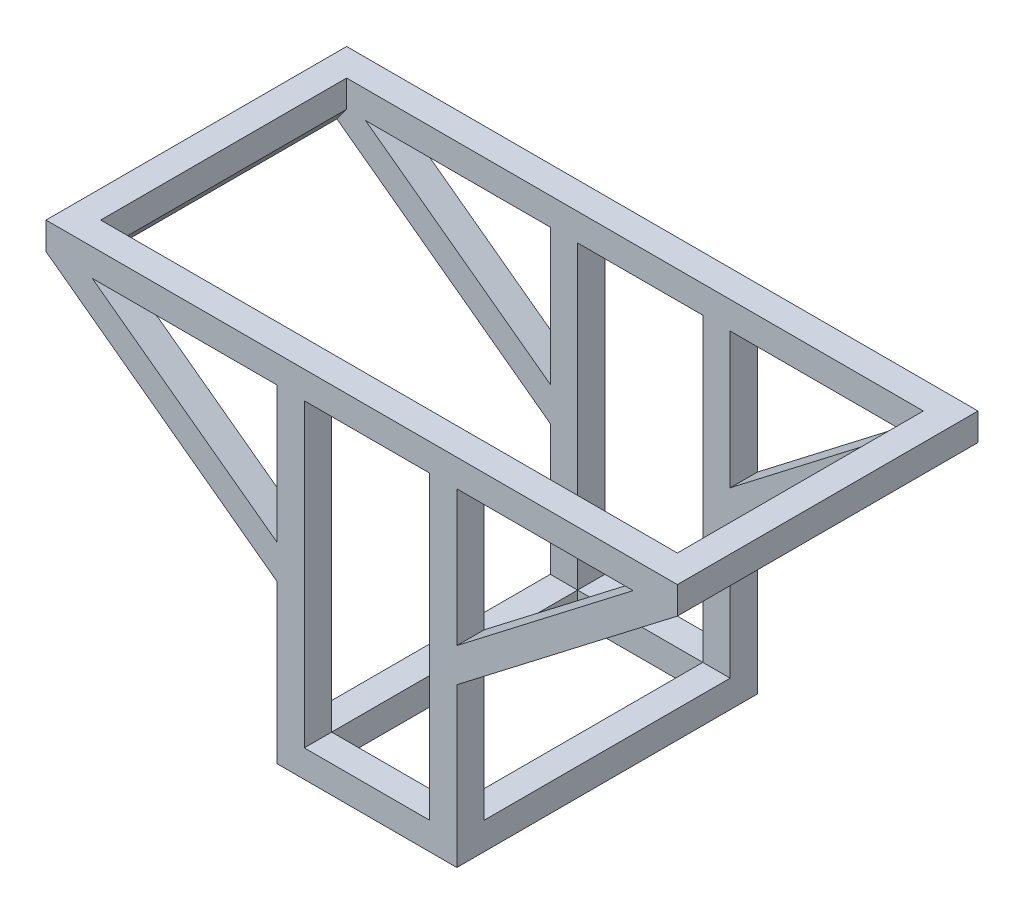
SolidWorks part; units mm, degrees
ref_plane "Front Plane" through (0, 0, 0) normal (0, 0, 1) x (1, 0, 0)
ref_plane "Top Plane" through (0, 0, 0) normal (0, 1, 0) x (1, 0, 0)
ref_plane "Right Plane" through (0, 0, 0) normal (1, 0, 0) x (0, 0, -1)
sketch "Sketch3" plane through (0, 0, 0) normal (0, 0, 1) x (1, 0, 0)
  line L0 (-115.5, 130) -> (115.5, 130)
  line L1 (115.5, 120) -> (34.82, 57.9186)
  line L2 (-31, 120) -> (-31, 70.1711)
  line L5 (-31, 0) -> (34.82, 0)
  line L6 (34.82, 0) -> (34.82, 57.9186)
  line L7 (-115.5, 130) -> (-115.5, 120)
  line L8 (115.5, 130) -> (115.5, 120)
  line L9 (-21, 10) -> (24.82, 10)
  line L10 (-98.5813, 120) -> (-31, 70.1711)
  line L11 (34.82, 70.3197) -> (34.82, 120)
  line L14 (-31, 0) -> (-31, 57.77)
  line L15 (-115.5, 120) -> (-31, 57.77)
  line L16 (115.5, 120) -> (34.82, 57.9186)
  line L17 (34.82, 70.3197) -> (99.3312, 120)
  line L18 (-31, 57.77) -> (-115.5, 120)
  line L19 (-21, 10) -> (-21, 120)
  line L20 (-98.5813, 120) -> (-31, 120)
  line L21 (24.82, 10) -> (24.82, 120)
  line L22 (-31, 70.1711) -> (-98.5813, 120)
  line L23 (-21, 120) -> (24.82, 120)
  line L24 (24.82, 10) -> (-21, 10)
  line L25 (-21, 120) -> (-21, 10)
  line L27 (99.3312, 120) -> (34.82, 70.3197)
  line L28 (34.82, 120) -> (99.3312, 120)
extrude "Extrude1" add sketch "Sketch3" along normal blind 110
sketch "Sketch5" plane through (-31, 0, 0) normal (-1, 0, 0) x (0, 0, 1)
  line L2 (10, 47.77) -> (100, 47.77)
  line L3 (10, 47.77) -> (10, 10)
  line L5 (10, 10) -> (100, 10)
  line L12 (100, 47.77) -> (100, 10)
extrude "Cut-Extrude1" cut sketch "Sketch5" against normal blind 72
sketch "Sketch6" plane through (0, 0, 0) normal (0, 1, 0) x (1, 0, 0)
  line L8 (24.82, -100) -> (-21, -100)
  line L9 (24.82, -100) -> (24.82, -10)
  line L10 (24.82, -10) -> (-21, -10)
  line L11 (-21, -100) -> (-21, -10)
extrude "Cut-Extrude3" cut sketch "Sketch6" along normal blind 130
sketch "Sketch8" plane through (0, 130, 0) normal (0, 1, 0) x (1, 0, 0)
  line L9 (-105.5, -10) -> (105.5, -10)
  line L10 (-105.5, -10) -> (-105.5, -100)
  line L11 (-105.5, -100) -> (105.5, -100)
  line L12 (105.5, -10) -> (105.5, -100)
extrude "Cut-Extrude4" cut sketch "Sketch8" against normal blind 20
sketch "Sketch9" plane through (-15.0432, 19.5499, 0) normal (0.6098, -0.7925, 0) x (0.7925, 0.6098, 0)
  line L5 (62.9166, 110) -> (62.9166, 0) construction
  line L9 (154.7172, 100) -> (62.9166, 100)
  line L10 (154.7172, 100) -> (154.7172, 10)
  line L11 (154.7172, 10) -> (62.9166, 10)
  line L12 (62.9166, 100) -> (62.9166, 10)
extrude "Cut-Extrude6" cut sketch "Sketch9" against normal blind 10
sketch "Sketch10" plane through (34.82, 0, 0) normal (1, 0, 0) x (0, 0, -1)
  line L0 (-100, 120) -> (-10, 120)
  line L1 (-100, 47.77) -> (-10, 47.77) construction
  line L2 (-100, 47.77) -> (-10, 47.77)
  line L10 (-100, 47.77) -> (-100, 120)
  line L12 (-10, 47.77) -> (-10, 120)
extrude "Cut-Extrude9" cut sketch "Sketch10" against normal blind 10
sketch "Sketch11" plane through (16.6833, 22.6537, 0) normal (-0.593, -0.8052, 0) x (0.8052, -0.593, 0)
  line L9 (-156.1666, 10) -> (-52.5473, 10)
  line L10 (-156.1666, 10) -> (-156.1666, 100)
  line L11 (-156.1666, 100) -> (-52.5473, 100)
  line L12 (-52.5473, 10) -> (-52.5473, 100)
extrude "Cut-Extrude11" cut sketch "Sketch11" against normal blind 20
sketch "Sketch12" plane through (-31, 0, 0) normal (-1, 0, 0) x (0, 0, 1)
  line L9 (10, 129.8029) -> (100, 129.8029)
  line L10 (10, 129.8029) -> (10, 47.77)
  line L11 (10, 47.77) -> (100, 47.77)
  line L12 (100, 129.8029) -> (100, 47.77)
extrude "Cut-Extrude13" cut sketch "Sketch12" against normal blind 20
